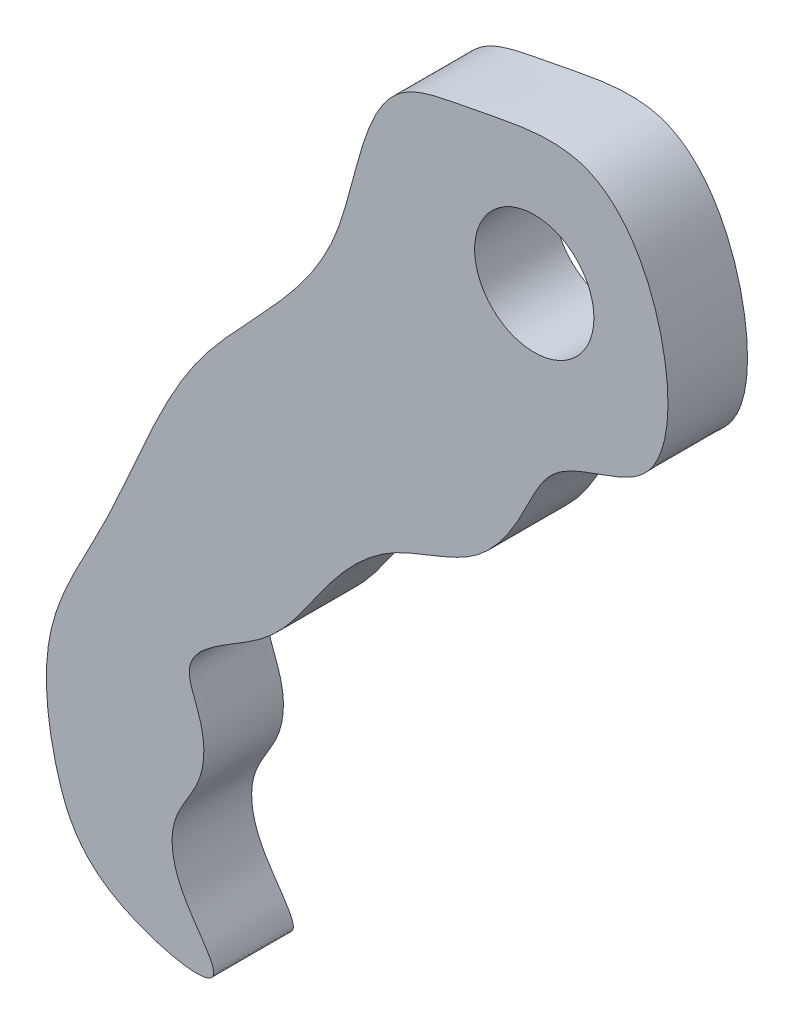
SolidWorks part; units mm, degrees
ref_plane "Front Plane" through (0, 0, 0) normal (0, 0, 1) x (1, 0, 0)
ref_plane "Top Plane" through (0, 0, 0) normal (0, 1, 0) x (1, 0, 0)
ref_plane "Right Plane" through (0, 0, 0) normal (1, 0, 0) x (0, 0, -1)
sketch "Sketch1" plane through (0, 0, 0) normal (0, 0, 1) x (1, 0, 0)
  line L0 (249.4347, 288.6021) -> (1247.1733, 288.6021) construction
  circle A0 centre (256.1749, 227.3256) radius 2.3813
  spline S0 degree 3 poles (241.7813, 199.2646) (244.7837, 196.046) (238.4823, 197.4408) (236.8783, 201.0526) (236.3643, 205.8748) (239.69, 211.211) (242.0608, 218.618) (249.0339, 223.525) (249.2932, 231.4161) (254.2556, 232.1644) (259.0206, 233.4102) (261.8648, 227.9426) (261.4002, 222.2062) (256.8543, 221.8823) (255.6723, 218.8267) (253.8303, 216.2482) (250.2364, 215.5009) (247.5605, 212.5104) (245.811, 209.3772) (241.7282, 207.8156) (243.0837, 205.3529) (243.0017, 203.4036) (241.5297, 201.6297) (241.7813, 199.2646) (244.7837, 196.046) (238.4823, 197.4408) knots -0.072708 -0.052767 -0.026612 0 0.04245 0.084451 0.1319 0.18556 0.278186 0.370887 0.444066 0.471112 0.520416 0.58303 0.631487 0.671779 0.698065 0.729106 0.768159 0.806912 0.849726 0.888524 0.904982 0.927292 0.947233 0.973388 1 1.04245 1.084451 1.1319 only from (243.3791, 197.0568) to (243.3791, 197.0568)
  dimension "D1" = 4.7625
extrude "Boss-Extrude1" add sketch "Sketch1" along normal blind 3.175 contours A0
ref_point "Point1" parameters "D1"=2.54
